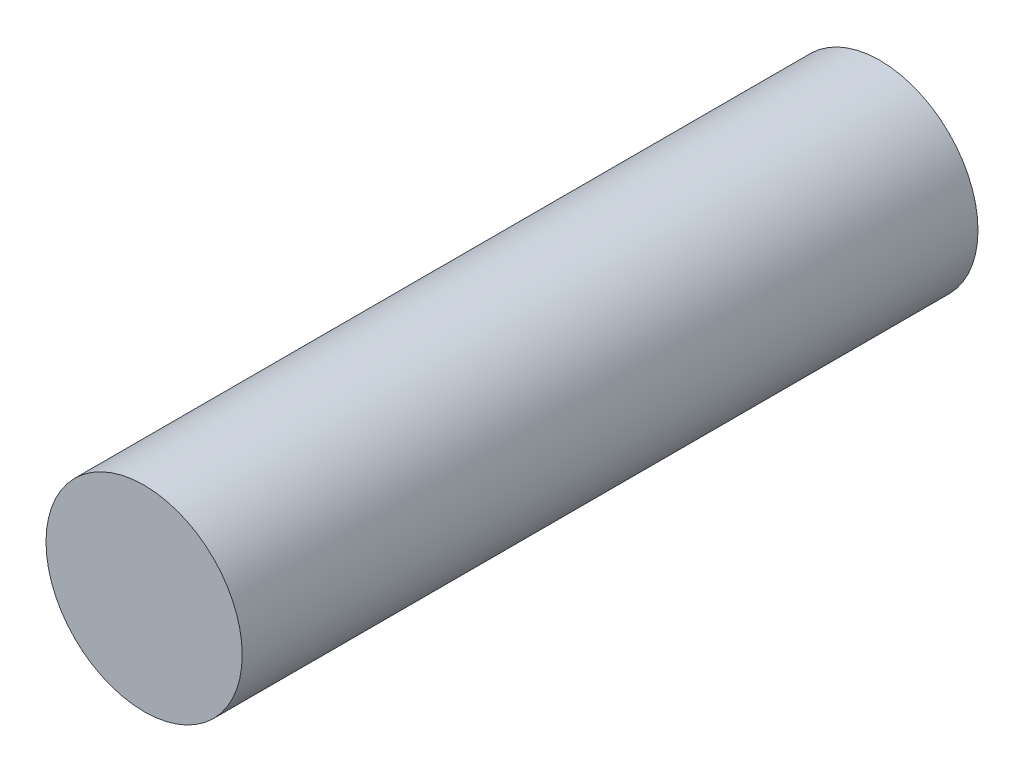
SolidWorks part; units mm, degrees
material "ABS"
ref_plane "Plan de face" through (0, 0, 0) normal (0, 0, 1) x (1, 0, 0)
ref_plane "Plan de dessus" through (0, 0, 0) normal (0, 1, 0) x (1, 0, 0)
ref_plane "Plan de droite" through (0, 0, 0) normal (1, 0, 0) x (0, 0, -1)
sketch "Esquisse1" plane through (0, 0, 0) normal (0, 0, 1) x (1, 0, 0)
  circle A0 centre (0, 0) radius 4
  dimension "D1" = 8
extrude "Boss.-Extru.1" add sketch "Esquisse1" along normal blind 30
